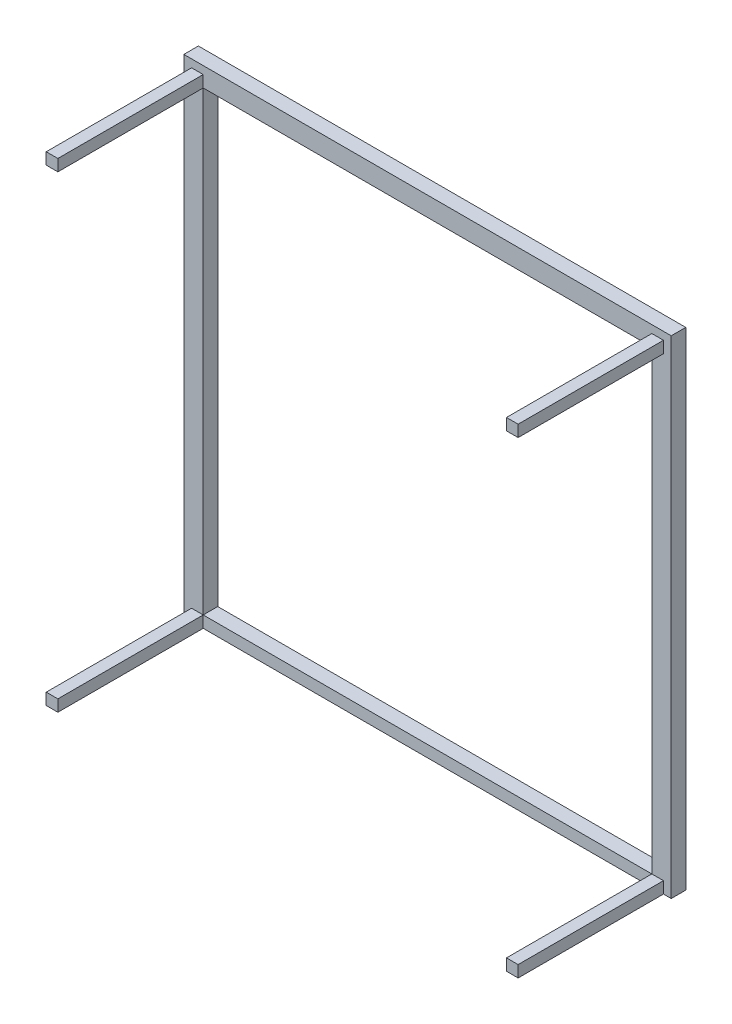
SolidWorks part; units mm, degrees
ref_plane "Front Plane" through (0, 0, 0) normal (0, 0, 1) x (1, 0, 0)
ref_plane "Top Plane" through (0, 0, 0) normal (0, 1, 0) x (1, 0, 0)
ref_plane "Right Plane" through (0, 0, 0) normal (1, 0, 0) x (0, 0, -1)
sketch "Sketch1" plane through (0, 0, 0) normal (0, 0, 1) x (1, 0, 0)
  line L1 (0, 0) -> (503, 0)
  line L2 (0, 0) -> (0, 503)
  line L3 (0, 503) -> (503, 503)
  line L4 (503, 0) -> (503, 503)
  line L5 (20, 483) -> (483, 483)
  line L6 (20, 483) -> (20, 12)
  line L7 (20, 12) -> (483, 12)
  line L8 (483, 483) -> (483, 12)
  dimension "D1" = 503
  dimension "D2" = 503
  dimension "D3" = 20
  dimension "D4" = 20
  dimension "D5" = 20
  dimension "D6" = 12
extrude "Boss-Extrude1" add sketch "Sketch1" along normal blind 15
sketch "Sketch2" plane through (0, 0, 15) normal (0, 0, 1) x (1, 0, 0)
  line L0 (0, 0) -> (503, 0) construction
  line L1 (20, 483) -> (8, 483)
  line L2 (20, 483) -> (20, 495)
  line L3 (20, 495) -> (8, 495)
  line L4 (8, 483) -> (8, 495)
  line L5 (483, 483) -> (495, 483)
  line L6 (483, 483) -> (483, 495)
  line L7 (483, 495) -> (495, 495)
  line L8 (495, 483) -> (495, 495)
  line L9 (20, 12) -> (8, 12)
  line L10 (20, 12) -> (20, 0)
  line L11 (20, 0) -> (8, 0)
  line L12 (8, 12) -> (8, 0)
  line L14 (483, 12) -> (495, 12)
  line L15 (483, 12) -> (483, 0)
  line L16 (483, 0) -> (495, 0)
  line L17 (495, 12) -> (495, 0)
  dimension "D1" = 12
  dimension "D2" = 12
  dimension "D3" = 12
  dimension "D4" = 12
  dimension "D5" = 12
extrude "Boss-Extrude2" add sketch "Sketch2" along normal blind 200
sketch "Sketch3" plane through (0, 0, 215) normal (0, 0, 1) x (1, 0, 0)
  line L1 (8, 495) -> (495, 495)
  line L2 (8, 495) -> (8, 0)
  line L3 (8, 0) -> (495, 0)
  line L4 (495, 495) -> (495, 0)
extrude "Cut-Extrude1" cut sketch "Sketch3" against normal blind 50
